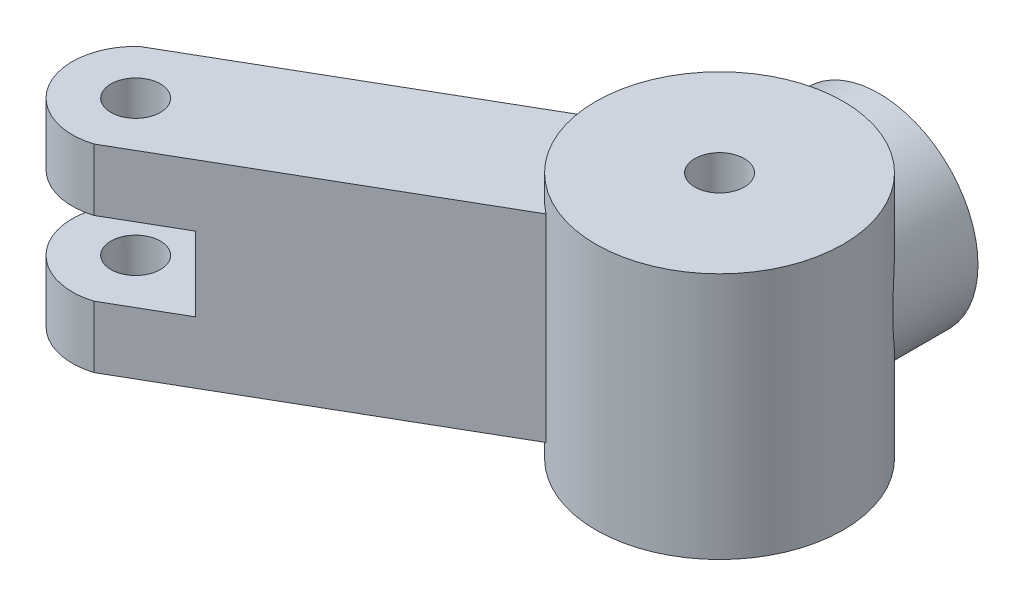
SolidWorks part; units mm, degrees
ref_plane "Front Plane" through (0, 0, 0) normal (0, 0, 1) x (1, 0, 0)
ref_plane "Top Plane" through (0, 0, 0) normal (0, 1, 0) x (1, 0, 0)
ref_plane "Right Plane" through (0, 0, 0) normal (1, 0, 0) x (0, 0, -1)
sketch "Sketch2" plane through (0, 0, 0) normal (0, 0, 1) x (1, 0, 0)
  circle A0 centre (0, 0) radius 2.5
  circle A1 centre (0, 0) radius 4
  dimension "D1" = 5
  dimension "D2" = 8
extrude "Boss-Extrude1" add sketch "Sketch2" along normal blind 4
sketch "Sketch3" plane through (0, 0, 4) normal (0, 0, 1) x (1, 0, 0)
  line L0 (0, 0) -> (0, 4.4418) construction
ref_plane "Plane1" through (0, 4.4418, 4) normal (0, 1, 0) x (1, 0, 0)
sketch "Sketch4" plane through (0, 4.4418, 4) normal (0, 1, 0) x (1, 0, 0)
  circle A0 centre (0, -2.4444) radius 5
  dimension "D1" = 10
extrude "Boss-Extrude2" add sketch "Sketch4" against normal blind 10
sketch "Sketch5" plane through (0, 0, 0) normal (0, 0, 1) x (1, 0, 0)
  circle A0 centre (0, 0) radius 2.5
  dimension "D1" = 5
extrude "Cut-Extrude1" cut sketch "Sketch5" along normal blind 5
sketch "Sketch6" plane through (0, 4.4418, 0) normal (0, 1, 0) x (1, 0, 0)
  circle A2 centre (0, -6.4444) radius 1
  dimension "D1" = 2
extrude "Cut-Extrude2" cut sketch "Sketch6" against normal through all
ref_plane "Plane4" through (-7.1206, 0, 4.1111) normal (-0.866, 0, 0.5) x (0, 1, 0)
sketch "Sketch7" plane through (-7.1206, 0, 4.1111) normal (-0.866, 0, 0.5) x (0, 1, 0)
  line L0 (4.4418, -10.581) -> (4.4418, -0.581) construction
  line L1 (3.4418, -2.4641) -> (-4.5582, -2.4641)
  line L2 (3.4418, -2.4641) -> (3.4418, -7.4641)
  line L3 (3.4418, -7.4641) -> (-4.5582, -7.4641)
  line L4 (-4.5582, -2.4641) -> (-4.5582, -7.4641)
  line L5 (-5.5582, -0.581) -> (-5.5582, -10.581) construction
  line L6 (0, -3.4641) -> (4.4418, -3.4641) construction
  dimension "D1" = 1
  dimension "D2" = 1
  dimension "D3" = 5
  dimension "D4" = 4
extrude "Boss-Extrude3" add sketch "Sketch7" along normal blind 15 and the other way up to surface
sketch "Sketch9" plane through (0, 3.4418, 0) normal (0, 1, 0) x (1, 0, 0)
  line L0 (-16.3789, -18.0752) -> (-3.0697, -10.3911) construction
  line L1 (-16.3789, -18.0752) -> (-18.8789, -13.7451) construction
  line L2 (-18.8789, -13.7451) -> (-4.9443, -5.6999) construction
  line L3 (-16.3789, -18.0752) -> (-14.6469, -17.0752)
  line L4 (-16.3789, -18.0752) -> (-18.8789, -13.7451)
  line L5 (-18.8789, -13.7451) -> (-17.1469, -12.7451)
  arc A0 (-17.1469, -12.7451) -> (-14.6469, -17.0752) centre (-15.4098, -14.6289) ccw
  circle A1 centre (-15.4098, -14.6289) radius 1
  point P8 (0, 0)
  point P9 (0, 0)
  point P10 (0, 0)
  point P11 (0, 0)
  point P12 (0, 0)
  point P13 (0, 0)
  line M2 (-16.3789, -18.0752) -> (-3.0697, -10.3911)
  line M4 (-4.9443, -5.6999) -> (-18.8789, -13.7451)
  line M5 (-18.8789, -13.7451) -> (-16.3789, -18.0752)
  dimension "D1" = 2
  dimension "D2" = 2.5
  dimension "D3" = 2
sketch "Sketch10" plane through (1.2321, 0, 2.134) normal (-0.5, 0, -0.866) x (-0.866, 0, 0.5)
  line L0 (23.2222, 3.4418) -> (23.2222, -4.5582) construction
  line L1 (23.2222, 0.9418) -> (18.2222, 0.9418)
  line L2 (23.2222, 0.9418) -> (23.2222, -2.0582)
  line L3 (23.2222, -2.0582) -> (18.2222, -2.0582)
  line L4 (18.2222, 0.9418) -> (18.2222, -2.0582)
  line L5 (23.2222, 3.4418) -> (7.1318, 3.4418) construction
  dimension "D1" = 3
  dimension "D2" = 2.5
  dimension "D3" = 5
extrude "Cut-Extrude4" cut sketch "Sketch10" against normal blind 20
extrude "Cut-Extrude6" cut sketch "Sketch9" against normal blind 20 contours A0 M4 M5 | A0 L4 M2 | A1
